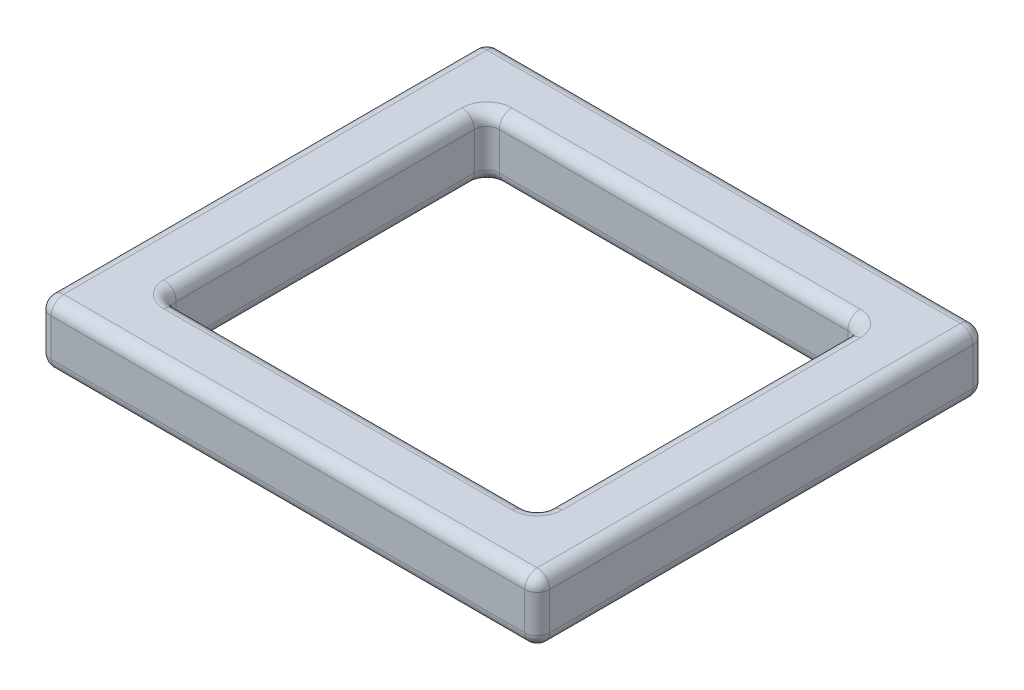
SolidWorks part; units mm, degrees
ref_plane "Front Plane" through (0, 0, 0) normal (0, 0, 1) x (1, 0, 0)
ref_plane "Top Plane" through (0, 0, 0) normal (0, 1, 0) x (1, 0, 0)
ref_plane "Right Plane" through (0, 0, 0) normal (1, 0, 0) x (0, 0, -1)
sketch "Sketch1" plane through (0, 0, 0) normal (0, 1, 0) x (1, 0, 0)
  line L0 (-31.8678, 24.8721) -> (-31.8678, -26.78)
  line L1 (-41.8678, 34.8721) -> (37.84, 34.8721)
  line L2 (-41.8678, 34.8721) -> (-41.8678, -36.78)
  line L3 (-41.8678, -36.78) -> (37.84, -36.78)
  line L4 (37.84, 34.8721) -> (37.84, -36.78)
  line L5 (-31.8678, -26.78) -> (27.84, -26.78)
  line L6 (27.84, 24.8721) -> (27.84, -26.78)
  line L7 (-31.8678, 24.8721) -> (27.84, 24.8721)
  dimension "D1" = 10
extrude "Extrude1" add sketch "Sketch1" along normal blind 10
fillet "Fillet1" radius 2
